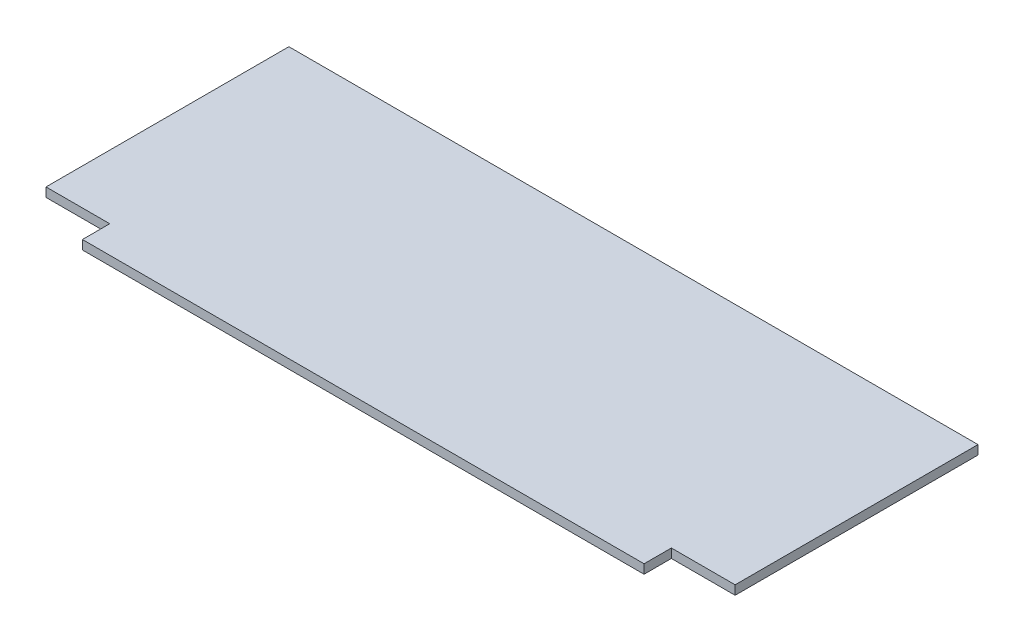
SolidWorks part; units mm, degrees
material "Benutzerdefinierter Kunststoff"
ref_plane "Plane Front" through (0, 0, 0) normal (0, 0, 1) x (1, 0, 0)
ref_plane "Plane Top" through (0, 0, 0) normal (0, 1, 0) x (1, 0, 0)
ref_plane "Plane Right" through (0, 0, 0) normal (1, 0, 0) x (0, 0, -1)
sketch "Sketch1" plane through (0, 0, 0) normal (0, 1, 0) x (1, 0, 0)
  line L1 (-113.5, -44.5) -> (113.5, -44.5)
  line L2 (-113.5, -44.5) -> (-113.5, 44.5)
  line L3 (-113.5, 44.5) -> (113.5, 44.5)
  line L4 (113.5, -44.5) -> (113.5, 44.5)
  line L5 (-113.5, -44.5) -> (113.5, 44.5) construction
  line L6 (-113.5, 44.5) -> (113.5, -44.5) construction
  line L7 (-113.5, -44.5) -> (-92.5, -44.5)
  line L8 (-113.5, -44.5) -> (-113.5, -35.5)
  line L9 (-113.5, -35.5) -> (-92.5, -35.5)
  line L10 (-92.5, -44.5) -> (-92.5, -35.5)
  line L11 (113.5, -44.5) -> (92.5, -44.5)
  line L12 (113.5, -44.5) -> (113.5, -35.5)
  line L13 (113.5, -35.5) -> (92.5, -35.5)
  line L14 (92.5, -44.5) -> (92.5, -35.5)
  point P0 (0, 0)
  dimension "D1" = 89
  dimension "D2" = 227
  dimension "D3" = 9
  dimension "D4" = 21
  dimension "D5" = 9
  dimension "D6" = 21
extrude "Extrude1" add sketch "Sketch1" along normal blind 3 contours L1 L14 L13 L4 L3 L2 L9 L10
